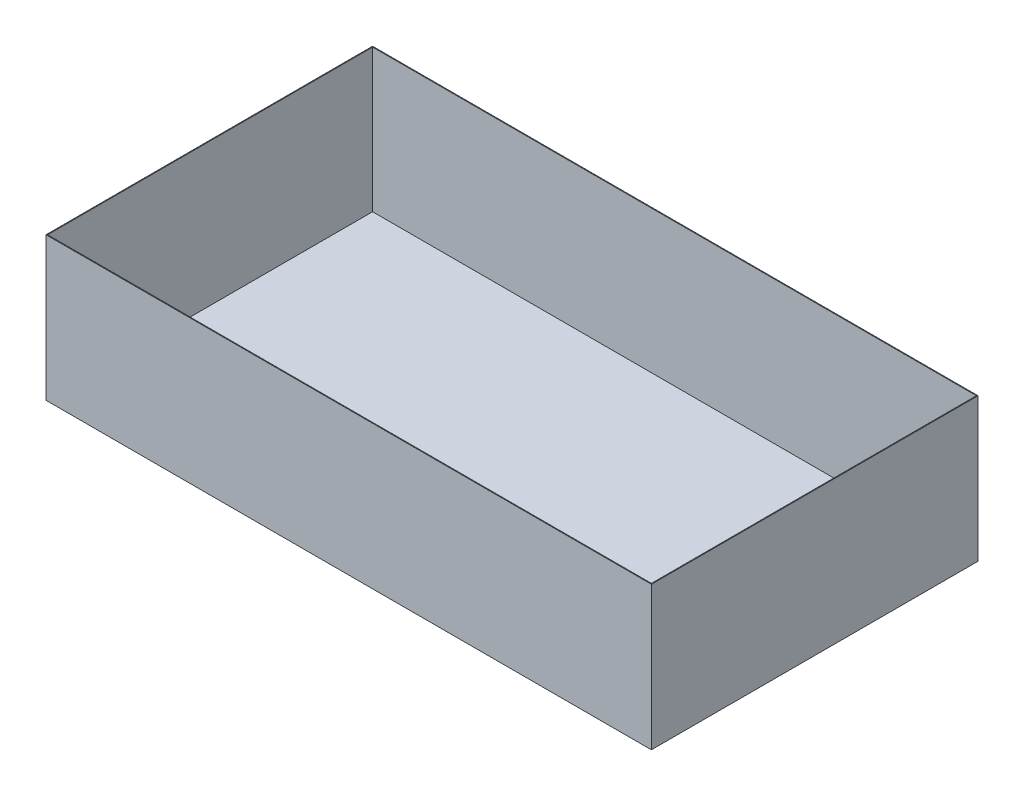
SolidWorks part; units mm, degrees
material "ABS PC"
ref_plane "Front Plane" through (0, 0, 0) normal (0, 0, 1) x (1, 0, 0)
ref_plane "Top Plane" through (0, 0, 0) normal (0, 1, 0) x (1, 0, 0)
ref_plane "Right Plane" through (0, 0, 0) normal (1, 0, 0) x (0, 0, -1)
sketch "Sketch1" plane through (0, 0, 0) normal (0, 1, 0) x (1, 0, 0)
  line L1 (-224.9762, 90.5803) -> (535.0238, 90.5803)
  line L2 (-224.9762, 90.5803) -> (-224.9762, -319.4197)
  line L3 (-224.9762, -319.4197) -> (535.0238, -319.4197)
  line L4 (535.0238, 90.5803) -> (535.0238, -319.4197)
  dimension "D1" = 760
  dimension "D2" = 410
extrude "Boss-Extrude1" add sketch "Sketch1" along normal blind 180
shell "Shell2" thickness 1
